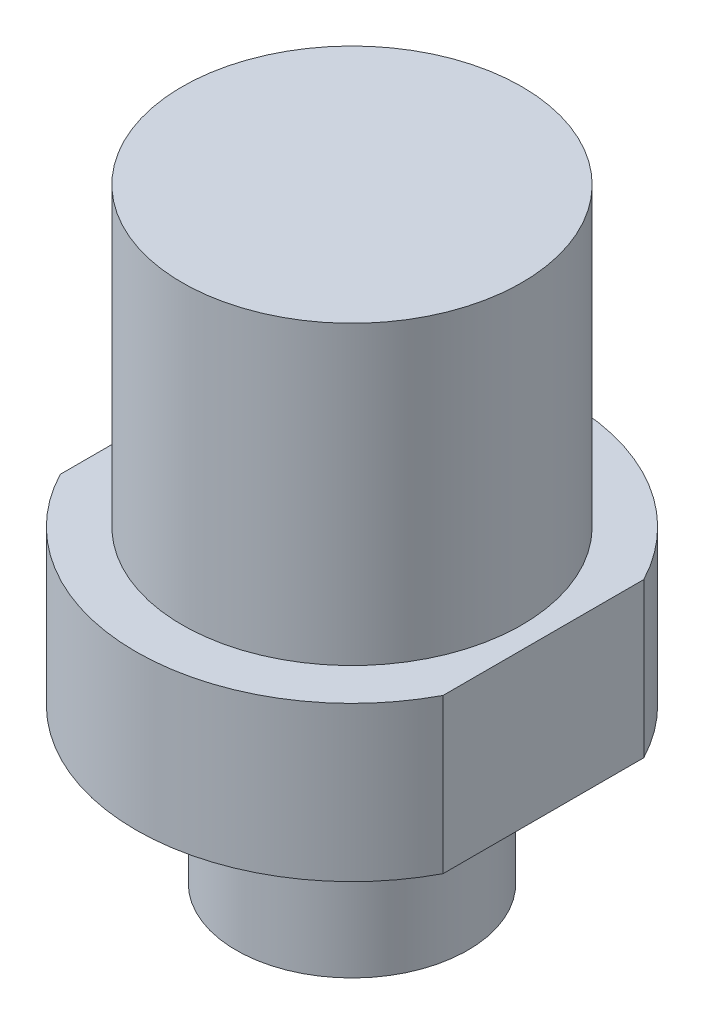
SolidWorks part; units mm, degrees
material "Cast Stainless Steel"
ref_plane "Front Plane" through (0, 0, 0) normal (0, 0, 1) x (1, 0, 0)
ref_plane "Top Plane" through (0, 0, 0) normal (0, 1, 0) x (1, 0, 0)
ref_plane "Right Plane" through (0, 0, 0) normal (1, 0, 0) x (0, 0, -1)
sketch "Sketch1" plane through (0, 0, 0) normal (1, 0, 0) x (0, 0, -1)
  line L0 (0, 0) -> (0, 18.542)
  line L1 (0, 18.542) -> (6.985, 18.542)
  line L2 (6.985, 18.542) -> (6.985, 6.35)
  line L3 (6.985, 6.35) -> (8.89, 6.35)
  line L4 (8.89, 6.35) -> (8.89, 0)
  line L5 (8.89, 0) -> (4.7625, 0)
  line L6 (4.7625, 0) -> (4.7625, -6.35)
  line L7 (4.7625, -6.35) -> (0, -6.35)
  line L8 (0, -6.35) -> (0, 0)
  dimension "D1" = 6.985
  dimension "D2" = 6.35
  dimension "D3" = 18.542
  dimension "D4" = 8.89
  dimension "D5" = 6.35
  dimension "D6" = 4.7625
revolve "Revolve1" add sketch "Sketch1" angle 360 about L0
sketch "Sketch2" plane through (0, 18.542, 0) normal (0, 1, 0) x (1, 0, 0)
  line L1 (-7.874, 8.89) -> (7.874, 8.89)
  line L2 (-7.874, 8.89) -> (-7.874, -8.89)
  line L3 (-7.874, -8.89) -> (7.874, -8.89)
  line L4 (7.874, 8.89) -> (7.874, -8.89)
  circle A0 centre (0, 0) radius 8.89 construction
  circle A1 centre (0, 0) radius 8.89
  point P4 (0, 8.89)
  dimension "D1" = 15.748
extrude "Cut-Extrude1" cut sketch "Sketch2" against normal through all contours L2 A1 | L4 A1
